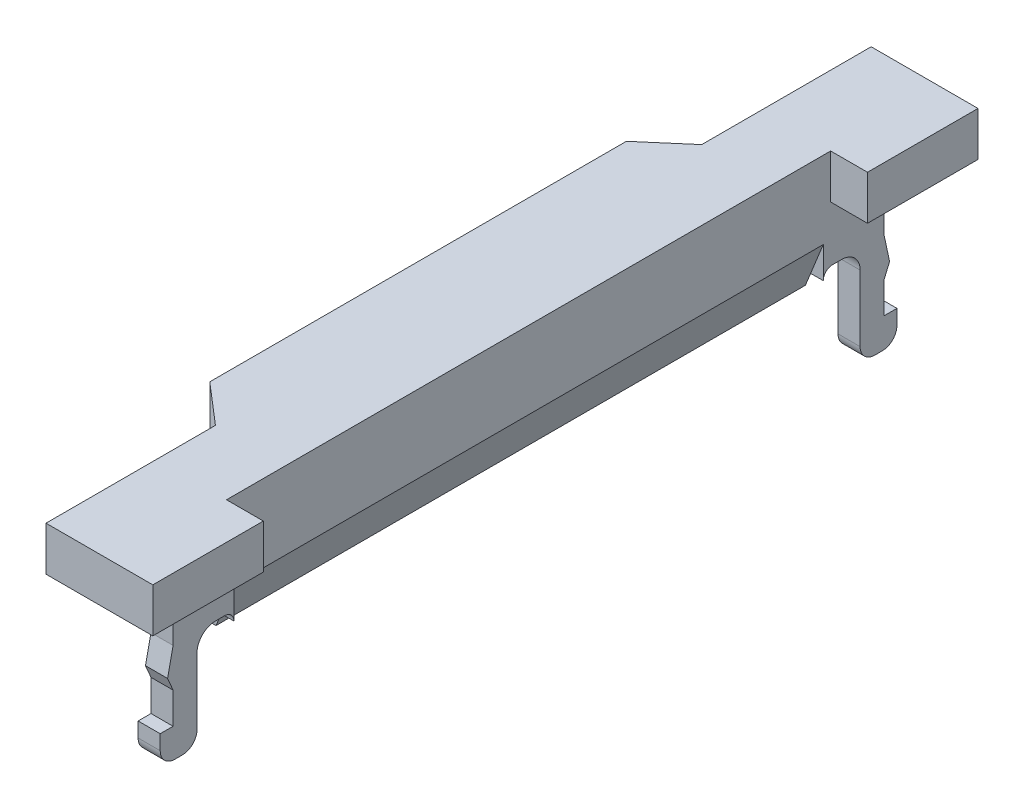
SolidWorks part; units mm, degrees
ref_plane "Plano frontal" through (0, 0, 0) normal (0, 0, 1) x (1, 0, 0)
ref_plane "Plano superior" through (0, 0, 0) normal (0, 1, 0) x (1, 0, 0)
ref_plane "Plano direito" through (0, 0, 0) normal (1, 0, 0) x (0, 0, -1)
sketch "Esboço1" plane through (0, 0, 0) normal (0, 1, 0) x (1, 0, 0)
  line L0 (2, 8.2) -> (2, 11.2)
  line L1 (-0.9, -11.2) -> (2, -11.2)
  line L2 (-2, -5.6547) -> (-2, 5.6547)
  line L3 (-0.9, 11.2) -> (2, 11.2)
  line L4 (2, -11.2) -> (2, -8.2)
  line L5 (-2, -11.2) -> (2, 11.2) construction
  line L6 (-2, 11.2) -> (2, -11.2) construction
  line L7 (2, 8.2) -> (1, 8.2)
  line L8 (-0.9, 11.2) -> (-0.9, 6.6)
  line L9 (2, -8.2) -> (1, -8.2)
  line L10 (1, 8.2) -> (1, -8.2)
  line L11 (-0.9, 6.6) -> (-2, 5.6547)
  line L13 (-2, -5.6547) -> (-0.9, -6.6)
  line L14 (-0.9, -6.6) -> (-0.9, -11.2)
  point P0 (0, 0)
  dimension "D1" = 22.4
  dimension "D2" = 4
  dimension "D3" = 1
  dimension "D4" = 16.4
  dimension "D5" = 8.2
  dimension "D6" = 2.9
  dimension "D7" = 2.9
  dimension "D8" = 13.2
  dimension "D9" = 6.6
extrude "Ressalto-extrusão1" add sketch "Esboço1" along normal blind 1.2
sketch "Esboço2" plane through (0, 0, 0) normal (0, -1, 0) x (1, 0, 0)
  line L0 (1, 8.2) -> (1, -8.2) construction
  line L1 (1, -8) -> (0.4, -8)
  line L2 (1, -8) -> (1, 8)
  line L3 (1, 8) -> (0.4, 8)
  line L4 (0.4, -8) -> (0.4, 8)
  dimension "D1" = 0.6
  dimension "D2" = 8
  dimension "D3" = 16
extrude "Ressalto-extrusão2" add sketch "Esboço2" along normal blind 2.1
chamfer "Chanfro1" distance 1.2 angle 22 1 edges at (1, -2.1, 0)
sketch "Esboço3" plane through (0.4, 0, 0) normal (-1, 0, 0) x (0, 0, 1)
  line L0 (-8.25, -1.5) -> (-8.5, -1.5)
  line L1 (-8, -2.1) -> (-8, 0) construction
  line L2 (-9, -2) -> (-9, -3.8)
  line L3 (-9.4, -4.2) -> (-9.6, -4.2)
  line L4 (-10, -3.8) -> (-10, -3.4)
  line L5 (-10, -3.4) -> (-9.65, -3.4)
  line L6 (-11.2, 0) -> (-6.6, 0) construction
  line L7 (-9.65, -3.4) -> (-9.65, -2.55)
  line L8 (-9.65, 0) -> (-8, 0)
  line L9 (-9.65, 0) -> (-9.85, -0.3)
  line L10 (-8, 0) -> (-8, -1.75)
  line L11 (-9.85, -0.3) -> (-9.85, -0.5)
  line L12 (-9.85, -0.5) -> (-9.65, -0.7)
  line L13 (-9.65, -1.5) -> (-9.8, -2.2)
  line L14 (-9.8, -2.2) -> (-9.65, -2.55)
  line L15 (-9.65, -1.5) -> (-9.65, -0.7)
  arc A0 (-8.25, -1.5) -> (-8, -1.75) centre (-8.25, -1.75) cw
  arc A1 (-8.5, -1.5) -> (-9, -2) centre (-8.5, -2) ccw
  arc A2 (-9.6, -4.2) -> (-10, -3.8) centre (-9.6, -3.8) cw
  arc A3 (-9, -3.8) -> (-9.4, -4.2) centre (-9.4, -3.8) cw
  point P17 (-9, -1.5)
  point P20 (-10, -4.2)
  point P23 (-9, -4.2)
  dimension "D1" = 0.25
  dimension "D9" = 0.5
  dimension "D11" = 0.4
  dimension "D2" = 1.5
  dimension "D3" = 2.7
  dimension "D4" = 1
  dimension "D5" = 0.8
  dimension "D6" = 0.35
  dimension "D7" = 0.25
  dimension "D8" = 0.25
  dimension "D10" = 1
  dimension "D12" = 0.3
  dimension "D13" = 0.2
  dimension "D14" = 0.2
  dimension "D15" = 0.2
  dimension "D16" = 1.5
  dimension "D17" = 0.7
  dimension "D18" = 0.15
  dimension "D19" = 0.35
extrude "Ressalto-extrusão3" add sketch "Esboço3" against normal up to surface (0.6 mm away) up to face at (1, -0.0375, 0.025)
mirror "Espelhar1" about plane through (0, 0, 0) normal (0, 0, 1) of "Ressalto-extrusão3"
